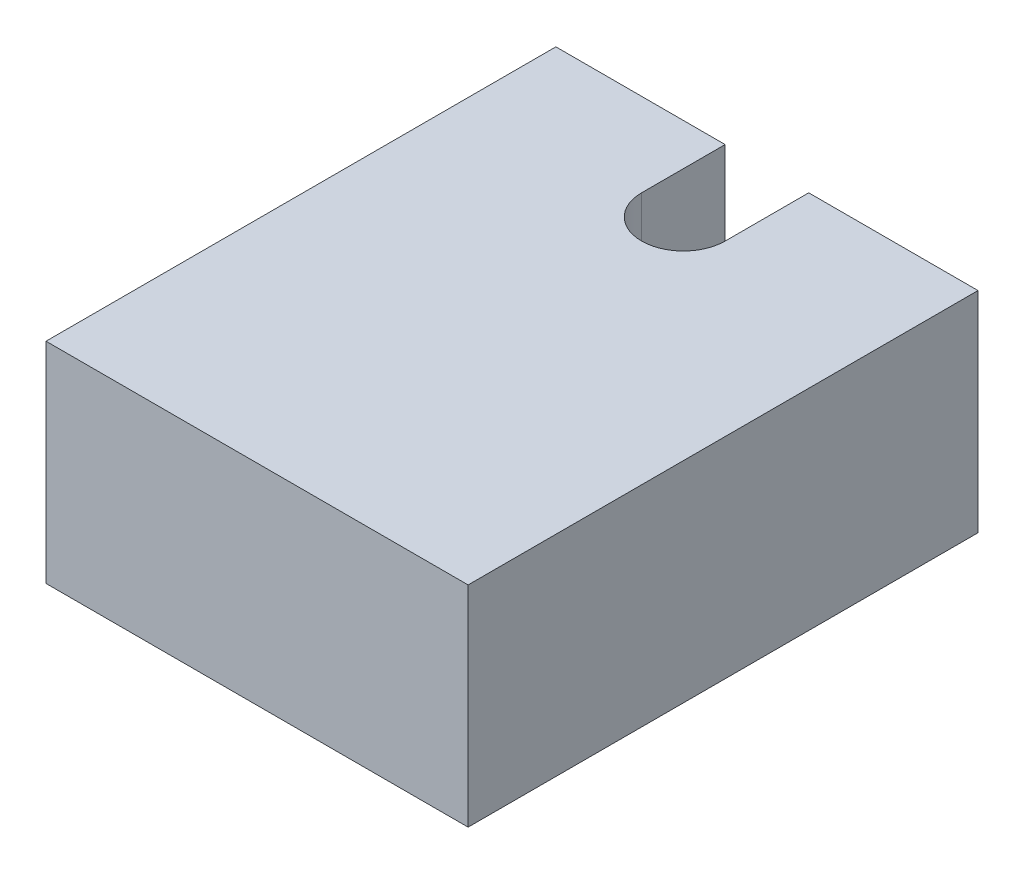
SolidWorks part; units mm, degrees
ref_plane "Plan de face" through (0, 0, 0) normal (0, 0, 1) x (1, 0, 0)
ref_plane "Plan de dessus" through (0, 0, 0) normal (0, 1, 0) x (1, 0, 0)
ref_plane "Plan de droite" through (0, 0, 0) normal (1, 0, 0) x (0, 0, -1)
sketch "Esquisse1" plane through (0, 0, 0) normal (0, 1, 0) x (1, 0, 0)
  line L0 (-25.0027, 0) -> (50.3609, 0) construction
  line L1 (0, -10.3092) -> (0, 33.2974) construction
  line L2 (-7.2283, 6.1) -> (17.8929, 6.1) construction
  line L3 (5.05, 24.2917) -> (5.05, -5.8063) construction
  line L4 (2.525, 9.5504) -> (2.525, 3.1172) construction
  line L5 (0.7186, 5.1) -> (8.911, 5.1) construction
  line L6 (2.025, 3.8962) -> (2.025, 7.2888) construction
  line L7 (3.025, 4.0721) -> (3.025, 6.9369) construction
  line L8 (3.025, 5.1) -> (3.025, 6.1)
  line L9 (3.025, 6.1) -> (5.05, 6.1)
  line L10 (5.05, 6.1) -> (5.05, 0)
  line L11 (5.05, 0) -> (0, 0)
  line L12 (0, 0) -> (0, 6.1)
  line L13 (0, 6.1) -> (2.025, 6.1)
  line L14 (2.025, 6.1) -> (2.025, 5.1)
  arc A0 (2.025, 5.1) -> (3.025, 5.1) centre (2.525, 5.1) ccw
  dimension "D1" = 5.05
  dimension "D2" = 6.1
  dimension "D3" = 2.525
  dimension "D4" = 1
extrude "Extrusion1" add sketch "Esquisse1" along normal blind 2.51
sketch "Esquisse2" plane through (2.025, 0, 0) normal (1, 0, 0) x (0, 0, -1)
  line L0 (5.1, 3.4084) -> (5.1, -0.9756) construction
  line L1 (6.1, 3.2541) -> (6.1, -0.9756) construction
  line L2 (7.7747, 1.255) -> (4.5349, 1.255) construction
  line L3 (6.8362, 0) -> (4.2263, 0) construction
  line L4 (5.6, 3.0999) -> (5.6, 1.0172) construction
  circle A0 centre (5.6, 1.255) radius 0.25
  dimension "D1" = 0.5
  dimension "D2" = 1.255
extrude "Extrusion2" add sketch "Esquisse2" along normal blind 1
